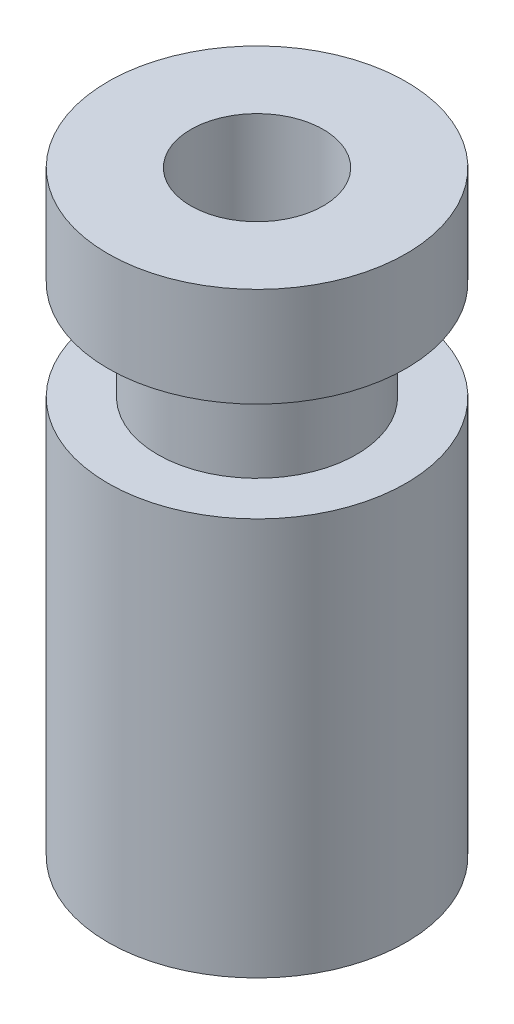
SolidWorks part; units mm, degrees
ref_plane "Front Plane" through (0, 0, 0) normal (0, 0, 1) x (1, 0, 0)
ref_plane "Top Plane" through (0, 0, 0) normal (0, 1, 0) x (1, 0, 0)
ref_plane "Right Plane" through (0, 0, 0) normal (1, 0, 0) x (0, 0, -1)
sketch "Sketch1" plane through (0, 0, 0) normal (0, 1, 0) x (1, 0, 0)
  circle A0 centre (0, 0) radius 2.25
  circle A1 centre (0, 0) radius 1
  dimension "D1" = 4.5
  dimension "D2" = 2
extrude "Boss-Extrude1" add sketch "Sketch1" along normal blind 6
sketch "Sketch2" plane through (0, 6, 0) normal (0, 1, 0) x (1, 0, 0)
  circle A0 centre (0, 0) radius 1 construction
  circle A1 centre (0, 0) radius 1
  circle A2 centre (0, 0) radius 1.5
  dimension "D1" = 3
extrude "Boss-Extrude2" add sketch "Sketch2" along normal blind 1.5
sketch "Sketch3" plane through (0, 7.5, 0) normal (0, 1, 0) x (1, 0, 0)
  circle A0 centre (0, 0) radius 1 construction
  circle A1 centre (0, 0) radius 1
  circle A2 centre (0, 0) radius 2.25 construction
  circle A3 centre (0, 0) radius 2.25
extrude "Boss-Extrude3" add sketch "Sketch3" along normal blind 1.5
